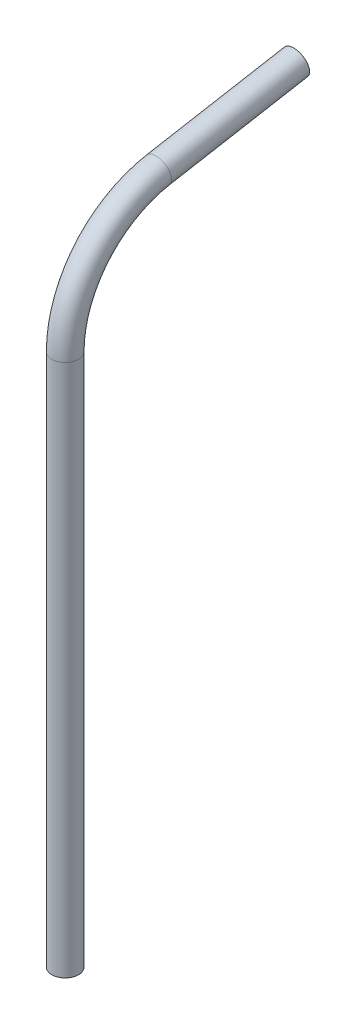
SolidWorks part; units mm, degrees
ref_plane "Front Plane" through (0, 0, 0) normal (0, 0, 1) x (1, 0, 0)
ref_plane "Top Plane" through (0, 0, 0) normal (0, 1, 0) x (1, 0, 0)
ref_plane "Right Plane" through (0, 0, 0) normal (1, 0, 0) x (0, 0, -1)
sketch "Sketch1" plane through (0, 0, 0) normal (0, 1, 0) x (1, 0, 0)
  circle A0 centre (0, 0) radius 2.667
  circle A1 centre (0, 0) radius 3.175
  dimension "D1" = 6.35
  dimension "D2" = 0.508
extrude "Boss-Extrude1" add sketch "Sketch1" along normal blind 127
sketch "Sketch2" plane through (0, 0, 0) normal (1, 0, 0) x (0, 0, -1)
  line L1 (3.175, 127) -> (-3.175, 127) construction
  line L2 (22.1666, 153.4567) -> (55.0128, 159.2983)
  line L3 (0, 127) -> (0, 121.8034) construction
  arc A0 (0, 127) -> (22.1666, 153.4567) centre (26.8718, 127) cw
  point P3 (23.7947, 153.6951)
  point P6 (55.0128, 159.2983)
sketch "Sketch3" plane through (0, 127, 0) normal (0, 1, 0) x (1, 0, 0)
  circle A0 centre (0, 0) radius 2.667 construction
  circle A1 centre (0, 0) radius 3.175
  circle A2 centre (0, 0) radius 3.175
  circle A3 centre (0, 0) radius 2.667
  dimension "D1" = 0
sweep "Sweep1" add profiles "Sketch3" path "Sketch2"
